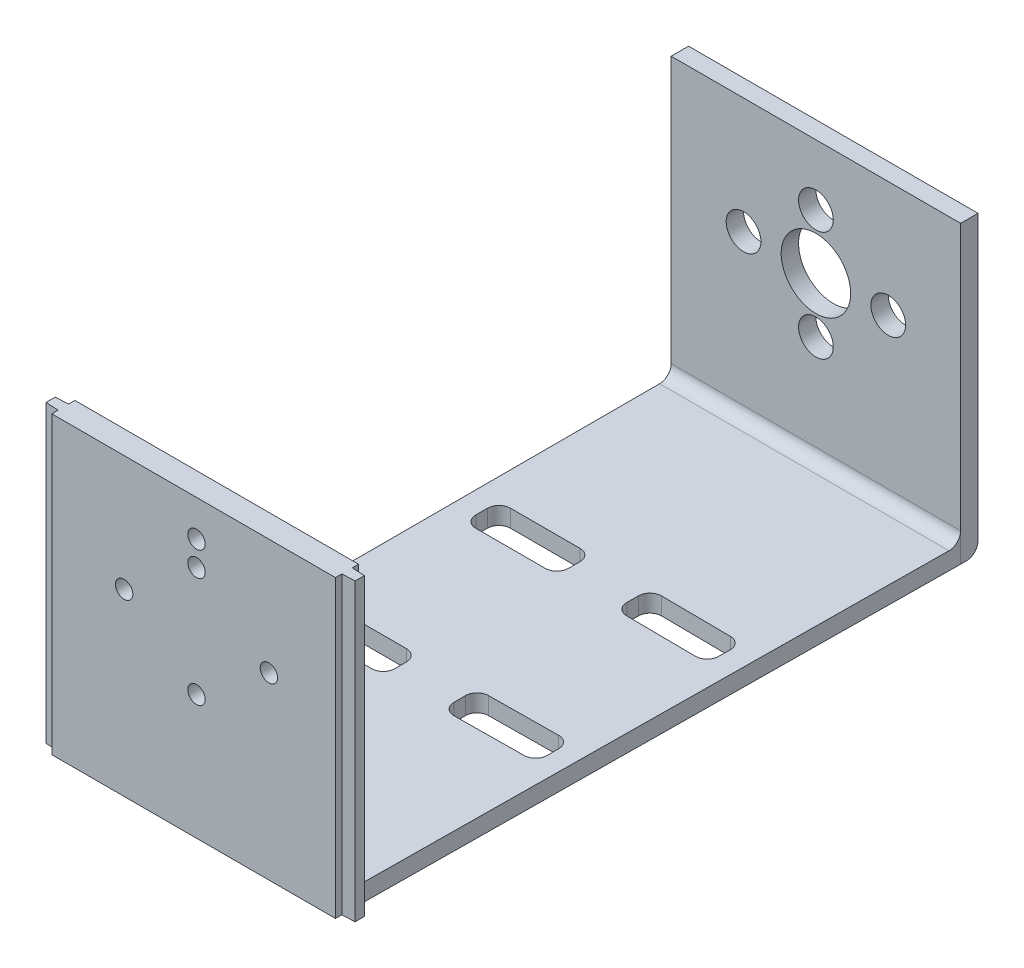
SolidWorks part; units mm, degrees
ref_plane "前视基准面" through (0, 0, 0) normal (0, 0, 1) x (1, 0, 0)
ref_plane "上视基准面" through (0, 0, 0) normal (0, 1, 0) x (1, 0, 0)
ref_plane "右视基准面" through (0, 0, 0) normal (1, 0, 0) x (0, 0, -1)
sketch "草图1" plane through (0, 0, 0) normal (0, 0, 1) x (1, 0, 0)
  line L0 (-25, 0) -> (-6, 0) construction
  line L2 (-25, 20) -> (-25, -31)
  line L3 (-25, -31) -> (25, -31)
  line L4 (25, 20) -> (25, -31)
  line L5 (-25, 31) -> (25, -31) construction
  line L6 (-25, -31) -> (23.9838, 29.7399) construction
  line L7 (-6, 0) -> (0, 0) construction
  line L8 (0, 0) -> (6, 0) construction
  line L9 (6, 0) -> (25, 0) construction
  line L10 (0, 31) -> (0, 0) construction
  line L11 (0, 0) -> (0, -6) construction
  line L12 (0, -6) -> (0, -31) construction
  line L13 (-25, 20) -> (25, 20)
  circle A0 centre (0, 0) radius 6
  circle A1 centre (12.5, 0) radius 3
  circle A2 centre (-12.5, 0) radius 3
  circle A3 centre (0, 9.5) radius 3
  circle A4 centre (0, -9.5) radius 3
  point P0 (0, 0)
  dimension "D3" = 12
  dimension "D5" = 6
  dimension "D6" = 6
  dimension "D8" = 6
  dimension "D1" = 49
  dimension "D2" = 62
  dimension "D4" = 25
  dimension "D7" = 12.5
  dimension "D9" = 9.5
  dimension "D10" = 51
extrude "凸台-拉伸1" add sketch "草图1" along normal blind 3
sketch "草图2" plane through (0, -31, 0) normal (0, -1, 0) x (1, 0, 0)
  line L0 (-25, 3) -> (-25, 106)
  line L1 (-25, 106) -> (24, 106)
  line L2 (24, 106) -> (25, 3)
  line L3 (-0.5, 106) -> (0, 3) construction
  line L4 (-25, 54.5) -> (-0.25, 54.5) construction
  line L5 (-0.25, 54.5) -> (24.5, 54.5) construction
  line L6 (-25, 3) -> (25, 3) construction
  line L7 (-25, 3) -> (25, 3)
  line L8 (-21.25, 42.5) -> (-5.25, 42.5)
  line L9 (-21.25, 42.5) -> (-21.25, 36.5)
  line L10 (-21.25, 36.5) -> (-5.25, 36.5)
  line L11 (-5.25, 42.5) -> (-5.25, 36.5)
  line L12 (-21.25, 42.5) -> (-5.25, 36.5) construction
  line L13 (-21.25, 36.5) -> (-5.25, 42.5) construction
  line L14 (4.8663, 42.5491) -> (4.9245, 36.5494)
  line L15 (20.9238, 36.7047) -> (4.9245, 36.5494)
  line L16 (20.8655, 42.7044) -> (20.9238, 36.7047)
  line L17 (20.8655, 42.7044) -> (4.8663, 42.5491)
  line L18 (-21.25, 66.5) -> (-21.25, 72.5)
  line L19 (-5.25, 66.5) -> (-5.25, 72.5)
  line L20 (-21.25, 72.5) -> (-5.25, 72.5)
  line L21 (-21.25, 66.5) -> (-5.25, 66.5)
  line L22 (20.8655, 66.2956) -> (20.9238, 72.2953)
  line L23 (20.9238, 72.2953) -> (4.9245, 72.4506)
  line L24 (4.8663, 66.4509) -> (4.9245, 72.4506)
  line L25 (20.8655, 66.2956) -> (4.8663, 66.4509)
  point P20 (-13.25, 39.5)
  dimension "D1" = 103
  dimension "D2" = 49
  dimension "D3" = 16
  dimension "D4" = 6
  dimension "D5" = 15
  dimension "D6" = 13
extrude "凸台-拉伸2" add sketch "草图2" against normal blind 3
sketch "草图3" plane through (0, 0, 106) normal (0, 0, 1) x (1, 0, 0)
  line L0 (24, 20) -> (-25, 20)
  line L1 (-25, -31) -> (24, -31)
  line L2 (-25, -31) -> (-25, 20)
  line L4 (24, -31) -> (24, 20)
  line L5 (24, -28) -> (-25, -28) construction
  circle A1 centre (-12.5, 0) radius 1.5
  circle A2 centre (12.5, 0) radius 1.5
  circle A3 centre (0, -9.5) radius 1.5
  circle A4 centre (0, 9.5) radius 1.5
  circle A5 centre (0, 13.75) radius 1.5
  dimension "D1" = 3
  dimension "D2" = 3
  dimension "D3" = 3
  dimension "D4" = 3
  dimension "D5" = 4.25
  dimension "D7" = 3
  dimension "D6" = 48
  dimension "D8" = 49
extrude "凸台-拉伸3" add sketch "草图3" along normal blind 4
fillet "圆角2" radius 2 1 edges at (-5.25, -29.5, 36.5)
fillet "圆角3" radius 2 3 edges at (-21.25, -29.5, 42.5) (-21.25, -29.5, 36.5) (-5.25, -29.5, 42.5)
fillet "圆角4" radius 2 12 edges at (-21.25, -29.5, 66.5) (-21.25, -29.5, 72.5) (-5.25, -29.5, 66.5) (-5.25, -29.5, 72.5) (4.9245, -29.5, 72.4506) (4.8663, -29.5, 66.4509) (20.9238, -29.5, 72.2953) (20.8655, -29.5, 66.2956) (4.8663, -29.5, 42.5491) (20.8655, -29.5, 42.7044) (20.9238, -29.5, 36.7047) (4.9245, -29.5, 36.5494)
fillet "圆角5" radius 2 1 edges at (0, -28, 3)
fillet "圆角6" radius 2 1 edges at (0, -31, 0)
ref_plane "基准面1" through (0, -31, 0) normal (0, -1, 0) x (-1, 0, 0)
sketch "草图6" plane through (0, -31, 0) normal (0, -1, 0) x (-1, 0, 0)
  line L0 (-24, -108.9) -> (-23.9893, -107.1)
  line L1 (-24, -110) -> (-24, -106) construction
  line L2 (-25, -3) -> (-24, -106) construction
  line L3 (25, -110) -> (-24, -110) construction
  line L4 (-23.9947, -108) -> (-27.9606, -108) construction
  line L5 (-26.2, -108.8) -> (-26.2, -107.2)
  line L6 (-26.2, -107.2) -> (-23.9893, -107.1)
  line L7 (-26.2, -108.8) -> (-24, -108.9)
  line L8 (0.5, -110) -> (0.5, -93.7477) construction
  line L9 (25, -108.9) -> (24.9893, -107.1)
  line L10 (27.2, -108.8) -> (25, -108.9)
  line L11 (27.2, -108.8) -> (27.2, -107.2)
  line L12 (27.2, -107.2) -> (24.9893, -107.1)
  point P13 (-26.2, -108)
  dimension "D1" = 1.1
  dimension "D2" = 1.8
  dimension "D3" = 1.6
  dimension "D4" = 2.2
extrude "凸台-拉伸5" add sketch "草图6" against normal blind 51
